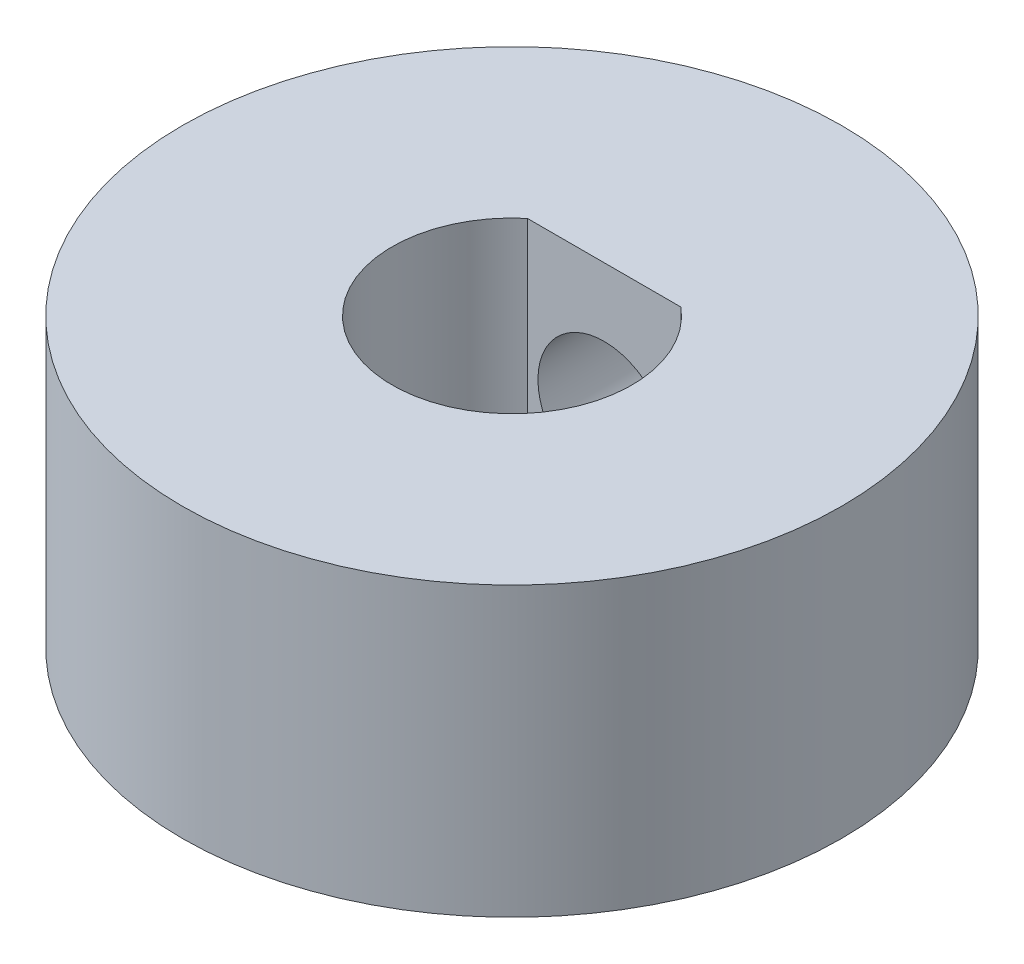
SolidWorks part; units mm, degrees
ref_plane "Front Plane" through (0, 0, 0) normal (0, 0, 1) x (1, 0, 0)
ref_plane "Top Plane" through (0, 0, 0) normal (0, 1, 0) x (1, 0, 0)
ref_plane "Right Plane" through (0, 0, 0) normal (1, 0, 0) x (0, 0, -1)
sketch "Sketch1" plane through (0, 0, 0) normal (0, 1, 0) x (1, 0, 0)
  line L0 (-2.032, 2.4396) -> (2.032, 2.4396)
  circle A0 centre (0, 0) radius 3.175
  circle A1 centre (0, 0) radius 8.7312
  dimension "D1" = 6.35
  dimension "D2" = 17.4625
  dimension "D3" = 4.064
extrude "Boss-Extrude1" add sketch "Sketch1" along normal blind 7.62 contours A1 A0 | L0 A0
ref_plane "Plane1" through (0, 0, -8.7312) normal (0, 0, -1) x (-1, 0, 0)
sketch "Sketch2" plane through (0, 0, -8.7312) normal (0, 0, -1) x (-1, 0, 0)
  line L0 (-8.7312, 0) -> (8.7312, 0) construction
  line L1 (8.7312, 0) -> (8.7312, 7.62) construction
  circle A0 centre (0, 4.064) radius 2.7686
  dimension "D1" = 5.5372
  dimension "D2" = 4.064
  dimension "D3" = 8.7312
extrude "Cut-Extrude1" cut sketch "Sketch2" against normal blind 3.81
sketch "Sketch3" plane through (0, 0, -4.9213) normal (0, 0, -1) x (-1, 0, 0)
  circle A0 centre (0, 4.064) radius 1.7526
  dimension "D1" = 3.5052
extrude "Cut-Extrude2" cut sketch "Sketch3" against normal up to next
